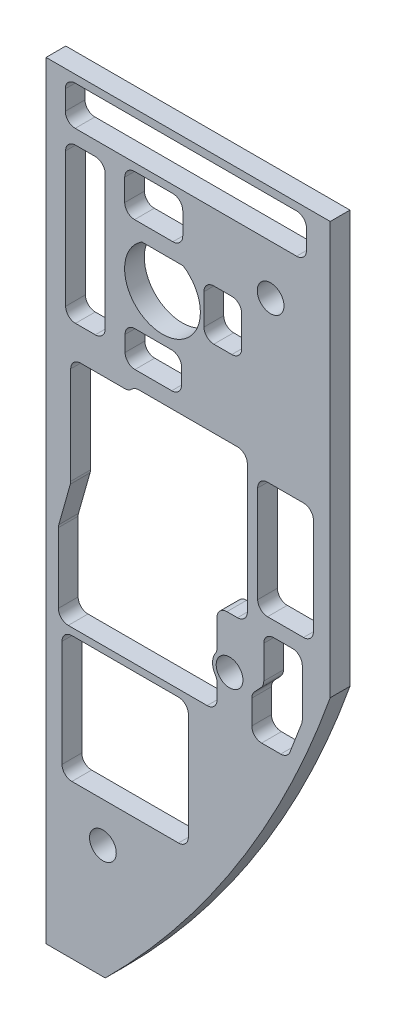
SolidWorks part; units mm, degrees
ref_plane "Front Plane" through (0, 0, 0) normal (0, 0, 1) x (1, 0, 0)
ref_plane "Top Plane" through (0, 0, 0) normal (0, 1, 0) x (1, 0, 0)
ref_plane "Right Plane" through (0, 0, 0) normal (1, 0, 0) x (0, 0, -1)
sketch "Sketch1" plane through (0, 0, 0) normal (0, 0, 1) x (1, 0, 0)
  line L8 (0, -17.78) -> (0, -141.2875)
  line L9 (0, -141.2875) -> (9.525, -141.2875)
  line L10 (45.72, -84.1375) -> (45.72, -17.78)
  line L11 (45.72, -17.78) -> (0, -17.78)
  circle A0 centre (18.7325, -40.894) radius 1.1901
  arc A2 (9.525, -141.2875) -> (45.72, -84.1375) centre (-97.9169, -33.2042) ccw
  circle A3 centre (18.7325, -40.894) radius 6.35 construction
extrude "Boss-Extrude1" add sketch "Sketch1" against normal blind 3.175
sketch "Sketch11" plane through (20.8448, -43.5748, 0) normal (0, 0, 1) x (1, 0, 0)
  line L0 (-5.4434, 7.7862) -> (1.2188, 7.7862)
  arc A0 (-5.4434, 7.7862) -> (1.2188, 7.7862) centre (-2.1123, 2.6808) ccw
  point P4 (-2.1123, -3.4152)
  dimension "D1" = 12.192
  dimension "D2" = 11.2014
extrude "Cut-Extrude1" cut sketch "Sketch11" against normal through all
other "Smart-Feature1<SxAL-1>"
sketch "Sketch12" plane through (0, 0, 0) normal (0, 0, 1) x (1, 0, 0)
  line L1 (13.335, -56.642) -> (32.385, -56.642)
  line L2 (13.335, -56.642) -> (13.335, -80.4545)
  line L3 (13.335, -80.4545) -> (32.385, -80.4545)
  line L4 (32.385, -56.642) -> (32.385, -80.4545)
  line L5 (22.86, -80.4545) -> (22.86, -56.642) construction
  line L6 (13.335, -68.5483) -> (32.385, -68.5483) construction
  point P152 (22.86, -68.5483)
extrude "Cut-Extrude2" cut sketch "Sketch12" against normal through all
hole_wizard "Hole1" [suppressed] positions "Sketch14" profile "Sketch13" legacy
sketch "Sketch14" plane through (0, 0, -3.175) normal (0, 0, -1) x (-1, 0, 0)
  point P0 (-34.29, -58.547)
  point P3 (-11.43, -78.5495)
  point P6 (-19.8535, -94.4687)
  point P8 (-5.5488, -118.2724)
sketch "Sketch13" plane through (34.29, -58.547, -3.175) normal (1, 0, 0) x (0, 1, 0)
  line L0 (0, 0) -> (0, 2.921)
  line L1 (0, 2.921) -> (1.4986, 2.921)
  line L2 (1.4986, 2.921) -> (1.6383, 0)
  line L3 (1.6383, 0) -> (0, 0)
  line L4 (0, 110) -> (0, -10) construction
  dimension "Minor Diameter" = 2.9972
  dimension "Depth" = 2.921
  dimension "Major Diameter" = 3.2766
hole_wizard "#2 Clearance Hole1" [suppressed] positions "Sketch16" profile "Sketch15" hole size "#2" standard "ANSI Inch"
sketch "Sketch16" [suppressed] plane through (0, 0, -0.254) normal (0, 0, -1) x (-1, 0, 0)
  point P0 (-34.29, -58.547)
  point P3 (-11.43, -78.5495)
sketch "Sketch15" plane through (34.29, -58.547, -0.254) normal (1, 0, 0) x (0, 1, 0)
  line L0 (0, 0) -> (0, 36.576)
  line L1 (0, 36.576) -> (1.3525, 36.576)
  line L2 (1.3525, 36.576) -> (1.3525, 0)
  line L5 (1.3525, 0) -> (0, 0)
  line L10 (0, 36.576) -> (-1.3526, 36.576) construction
  line L11 (0, -6.35) -> (0, 107.95) construction
  dimension "Hole Dia." = 2.7051
  dimension "Hole Depth" = 36.576
  dimension "Drill Angle" = 180
sketch "Sketch17" plane through (0, 0, 0) normal (0, 0, 1) x (1, 0, 0)
  line L1 (22.8917, -116.5825) -> (2.5717, -116.5825)
  line L2 (22.8917, -116.5825) -> (22.8917, -96.2625)
  line L3 (22.8917, -96.2625) -> (2.5717, -96.2625)
  line L4 (2.5717, -116.5825) -> (2.5717, -96.2625)
  line L5 (12.7317, -96.2625) -> (12.7317, -116.5825) construction
  line L6 (22.8917, -106.4225) -> (2.5717, -106.4225) construction
  point P192 (12.7317, -106.4225)
  dimension "D1" = 20.32
  dimension "D2" = 20.32
extrude "Cut-Extrude3" cut sketch "Sketch17" against normal through all
fillet "Fillet1" radius 1.5875 8 edges at (32.385, -56.642, -1.5875) (32.385, -80.4545, -1.5875) (13.335, -56.642, -1.5875) (13.335, -80.4545, -1.5875) (2.5717, -116.5825, -1.5875) (22.8917, -116.5825, -1.5875) (22.8917, -96.2625, -1.5875) (2.5717, -96.2625, -1.5875)
hole_wizard "#6 Clearance Hole1" positions "Sketch19" profile "Sketch18" hole size "#6" standard "ANSI Inch" end condition through all
sketch "Sketch19" plane through (0, 0, 0) normal (0, 0, 1) x (1, 0, 0)
  point P0 (9.144, -122.9995)
  point P3 (29.5275, -88.7095)
  point P6 (36.1315, -33.274)
sketch "Sketch18" plane through (9.144, -122.9995, 0) normal (1, 0, 0) x (0, -1, 0)
  line L0 (0, 0) -> (0, 3.175)
  line L1 (0, 3.175) -> (2.1526, 3.175)
  line L2 (2.1526, 3.175) -> (2.1526, 0)
  line L5 (2.1526, 0) -> (0, 0)
  line L11 (0, -6.35) -> (0, 107.95) construction
  dimension "Thru Hole Dia." = 4.3053
  dimension "Thru Hole Depth" = 3.175
sketch "Sketch20" plane through (0, 0, 0) normal (0, 0, 1) x (1, 0, 0)
  line L0 (1.9876, -93.5441) -> (1.9876, -82.3034)
  line L3 (25.9235, -95.1316) -> (3.5751, -95.1316)
  line L4 (39.2397, -94.9521) -> (41.1195, -90.0668)
  line L5 (41.2254, -89.4967) -> (41.2254, -81.903)
  line L6 (39.6379, -80.3155) -> (36.6148, -80.3155)
  line L7 (35.0273, -81.903) -> (35.0273, -87.1803)
  line L8 (34.6024, -88.2612) -> (33.5205, -89.4249)
  line L9 (33.0957, -90.5058) -> (33.0957, -94.382)
  line L10 (34.6832, -95.9695) -> (37.7581, -95.9695)
  line L12 (3.9669, -74.8629) -> (3.9669, -59.1889)
  line L13 (5.5544, -57.6014) -> (9.1171, -57.6014)
  line L19 (27.511, -91.1027) -> (27.511, -93.5441)
  line L20 (20.217, -54.1161) -> (14.3064, -54.1161)
  line L21 (12.7189, -52.5286) -> (12.7189, -50.0137)
  line L22 (14.3064, -48.4262) -> (20.217, -48.4262)
  line L23 (21.8045, -50.0137) -> (21.8045, -52.5286)
  line L24 (29.8851, -44.2376) -> (26.9962, -44.2376)
  line L25 (25.4087, -42.6501) -> (25.4087, -37.7142)
  line L26 (26.9962, -36.1267) -> (29.8851, -36.1267)
  line L27 (31.4726, -37.7142) -> (31.4726, -42.6501)
  line L28 (20.4069, -33.2591) -> (14.244, -33.2591)
  line L29 (12.6565, -31.6716) -> (12.6565, -28.1364)
  line L30 (14.244, -26.5489) -> (20.4069, -26.5489)
  line L31 (21.9944, -28.1364) -> (21.9944, -31.6716)
  line L32 (9.5117, -50.8817) -> (9.5117, -29.221)
  line L33 (7.9242, -27.6335) -> (4.7369, -27.6335)
  line L34 (3.1494, -29.221) -> (3.1494, -50.8817)
  line L35 (4.7369, -52.4692) -> (7.9242, -52.4692)
  line L36 (40.3131, -25.3216) -> (4.6847, -25.3216)
  line L37 (3.0972, -23.7341) -> (3.0972, -20.6064)
  line L38 (4.6847, -19.0189) -> (40.3131, -19.0189)
  line L39 (41.9006, -20.6064) -> (41.9006, -23.7341)
  line L44 (2.0474, -81.8715) -> (3.907, -75.2948)
  line L49 (27.511, -86.3141) -> (27.511, -57.6014)
  line L50 (27.511, -57.6014) -> (9.1171, -57.6014)
  line L51 (43.014, -76.3024) -> (43.014, -60.7403)
  line L52 (41.4265, -59.1528) -> (35.6378, -59.1528)
  line L53 (34.0503, -60.7403) -> (34.0503, -76.3024)
  line L54 (35.6378, -77.8899) -> (41.4265, -77.8899)
  arc A2 (1.9876, -93.5441) -> (3.5751, -95.1316) centre (3.5751, -93.5441) ccw
  arc A3 (27.511, -93.5441) -> (25.9235, -95.1316) centre (25.9235, -93.5441) cw
  arc A4 (41.1195, -90.0668) -> (41.2254, -89.4967) centre (39.6379, -89.4967) ccw
  arc A5 (39.2397, -94.9521) -> (37.7581, -95.9695) centre (37.7581, -94.382) cw
  arc A6 (33.0957, -94.382) -> (34.6832, -95.9695) centre (34.6832, -94.382) ccw
  arc A7 (33.5205, -89.4249) -> (33.0957, -90.5058) centre (34.6832, -90.5058) ccw
  arc A8 (35.0273, -87.1803) -> (34.6024, -88.2612) centre (33.4398, -87.1803) cw
  arc A9 (36.6148, -80.3155) -> (35.0273, -81.903) centre (36.6148, -81.903) ccw
  arc A10 (39.6379, -80.3155) -> (41.2254, -81.903) centre (39.6379, -81.903) cw
  arc A11 (3.9669, -59.1889) -> (5.5544, -57.6014) centre (5.5544, -59.1889) cw
  arc A17 (27.2445, -87.1946) -> (27.2445, -90.2223) centre (29.5158, -88.7084) ccw
  arc A18 (20.217, -48.4262) -> (21.8045, -50.0137) centre (20.217, -50.0137) cw
  arc A19 (12.7189, -50.0137) -> (14.3064, -48.4262) centre (14.3064, -50.0137) cw
  arc A20 (14.3064, -54.1161) -> (12.7189, -52.5286) centre (14.3064, -52.5286) cw
  arc A21 (20.217, -54.1161) -> (21.8045, -52.5286) centre (20.217, -52.5286) ccw
  arc A22 (29.8851, -36.1267) -> (31.4726, -37.7142) centre (29.8851, -37.7142) cw
  arc A23 (25.4087, -37.7142) -> (26.9962, -36.1267) centre (26.9962, -37.7142) cw
  arc A24 (26.9962, -44.2376) -> (25.4087, -42.6501) centre (26.9962, -42.6501) cw
  arc A25 (29.8851, -44.2376) -> (31.4726, -42.6501) centre (29.8851, -42.6501) ccw
  arc A26 (20.4069, -26.5489) -> (21.9944, -28.1364) centre (20.4069, -28.1364) cw
  arc A27 (12.6565, -28.1364) -> (14.244, -26.5489) centre (14.244, -28.1364) cw
  arc A28 (14.244, -33.2591) -> (12.6565, -31.6716) centre (14.244, -31.6716) cw
  arc A29 (20.4069, -33.2591) -> (21.9944, -31.6716) centre (20.4069, -31.6716) ccw
  arc A30 (4.7369, -27.6335) -> (3.1494, -29.221) centre (4.7369, -29.221) ccw
  arc A31 (9.5117, -29.221) -> (7.9242, -27.6335) centre (7.9242, -29.221) ccw
  arc A32 (9.5117, -50.8817) -> (7.9242, -52.4692) centre (7.9242, -50.8817) cw
  arc A33 (3.1494, -50.8817) -> (4.7369, -52.4692) centre (4.7369, -50.8817) ccw
  arc A34 (4.6847, -25.3216) -> (3.0972, -23.7341) centre (4.6847, -23.7341) cw
  arc A35 (3.0972, -20.6064) -> (4.6847, -19.0189) centre (4.6847, -20.6064) cw
  arc A36 (41.9006, -20.6064) -> (40.3131, -19.0189) centre (40.3131, -20.6064) ccw
  arc A37 (40.3131, -25.3216) -> (41.9006, -23.7341) centre (40.3131, -23.7341) ccw
  arc A38 (27.2445, -87.1946) -> (27.511, -86.3141) centre (25.9235, -86.3141) ccw
  arc A39 (27.2445, -90.2223) -> (27.511, -91.1027) centre (25.9235, -91.1027) cw
  arc A42 (3.9669, -74.8629) -> (3.907, -75.2948) centre (2.3794, -74.8629) cw
  arc A43 (1.9876, -82.3034) -> (2.0474, -81.8715) centre (3.5751, -82.3034) cw
  arc A44 (35.6378, -59.1528) -> (34.0503, -60.7403) centre (35.6378, -60.7403) ccw
  arc A45 (43.014, -60.7403) -> (41.4265, -59.1528) centre (41.4265, -60.7403) ccw
  arc A46 (43.014, -76.3024) -> (41.4265, -77.8899) centre (41.4265, -76.3024) cw
  arc A47 (34.0503, -76.3024) -> (35.6378, -77.8899) centre (35.6378, -76.3024) ccw
  point P42 (34.0542, -58.259)
  point P53 (10.7046, -69.3387)
  point P122 (27.511, -90.5608)
  point P124 (12.7189, -78.0896)
  dimension "D2" = 1.5875
  dimension "D3" = 1.5875
  dimension "D4" = 1.5875
  dimension "D5" = 1.5875
  dimension "D6" = 1.5875
  dimension "D7" = 1.5875
  dimension "D8" = 1.5875
  dimension "D9" = 1.5875
  dimension "D10" = 1.5875
  dimension "D11" = 1.5875
extrude "Cut-Extrude4" cut sketch "Sketch20" against normal through all
fillet "Fillet3" radius 1.5875 2 edges at (13.4645, -57.6014, -1.5875) (27.511, -80.4545, -1.5875)
